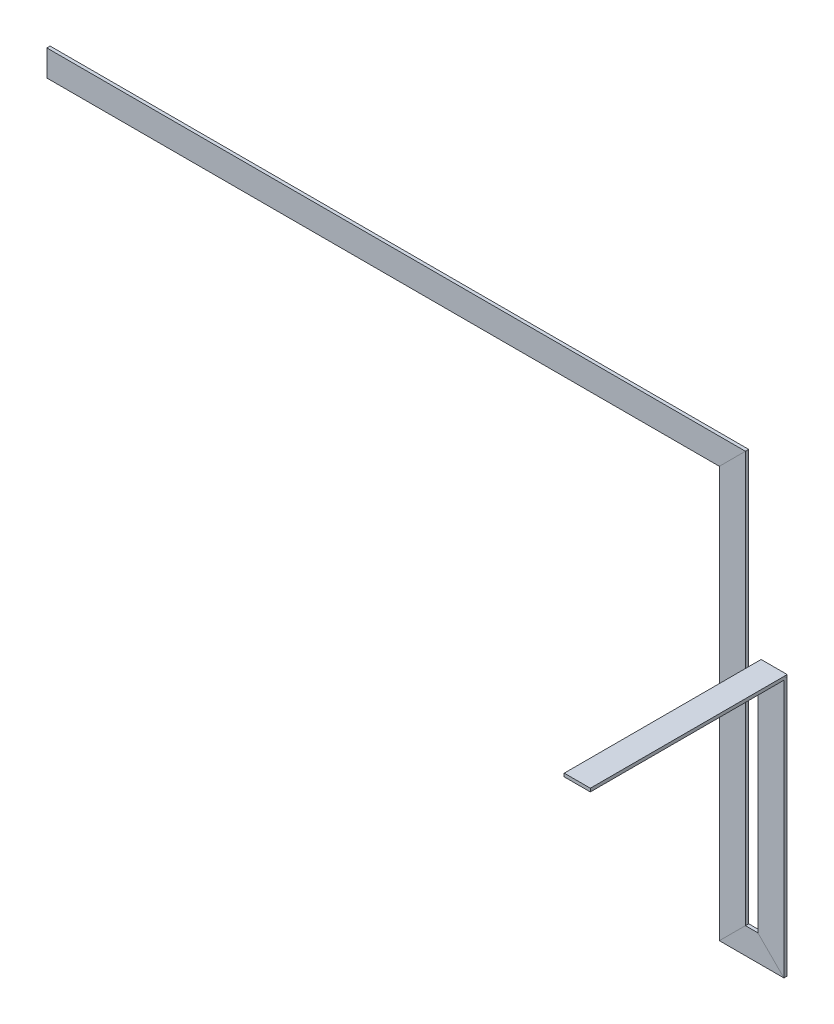
SolidWorks part; units mm, degrees
ref_plane "Alzado" through (0, 0, 0) normal (0, 0, 1) x (1, 0, 0)
ref_plane "Planta" through (0, 0, 0) normal (0, 1, 0) x (1, 0, 0)
ref_plane "Vista lateral" through (0, 0, 0) normal (1, 0, 0) x (0, 0, -1)
sketch3d "Croquis3D2"
  line L0 (62.2909, 217.5, 0) -> (62.2909, -251.2055, 0) construction
  line L1 (62.2909, -251.2055, 0) -> (-13.6009, -251.2055, 0) construction
  line L2 (-13.6009, -251.2055, 0) -> (-13.6009, 422.1421, 0) construction
  line L3 (-227.7091, 422.5, -94.9926) -> (-101.7371, 422.5, -94.9926) construction
  line L4 (-13.6009, 422.1421, 0) -> (-13.6009, 482.7109, 0) construction
  line L5 (-13.6009, 482.7109, 0) -> (-1290.2449, 482.7109, 0) construction
  line L6 (62.2909, 217.5, 0) -> (62.2909, 217.5, 73.9146)
  line L7 (62.2909, 217.5, 73.9146) -> (62.2909, -262.5, 73.9146)
  line L8 (62.2909, -262.5, 73.9146) -> (-12.7091, -262.5, 73.9146)
  line L9 (-12.7091, -262.5, 73.9146) -> (-12.7091, 537.5, 73.9146)
  line L10 (-12.7091, 537.5, 73.9146) -> (-1347.7009, 537.5, 73.9146)
  dimension "D1" = 800
  dimension "D2" = 75
  dimension "D3" = 480
  dimension "D4" = 1334.9917
sketch "Croquis3" plane through (0, 0, 0) normal (0, 0, 1) x (1, 0, 0)
  line L1 (36.8909, 220.675) -> (87.6909, 220.675)
  line L2 (36.8909, 220.675) -> (36.8909, 214.325)
  line L3 (36.8909, 214.325) -> (87.6909, 214.325)
  line L4 (87.6909, 220.675) -> (87.6909, 214.325)
  line L5 (36.8909, 220.675) -> (87.6909, 214.325) construction
  line L6 (36.8909, 214.325) -> (87.6909, 220.675) construction
  point P0 (62.2909, 217.5)
  dimension "D1" = 50.8
  dimension "D2" = 6.35
sweep "Barrer1" add profiles "Croquis3" path "Croquis3D2"
ref_plane "Plano1" through (62.2909, 0, 0) normal (1, 0, 0) x (0, 0, -1)
sketch "Croquis4" plane through (0, 0, 77.0896) normal (0, 0, 1) x (1, 0, 0)
  line L0 (36.8909, 220.675) -> (36.8909, 214.325)
  line L1 (36.8909, 214.325) -> (87.6909, 214.325)
  line L2 (87.6909, 214.325) -> (87.6909, 220.675)
  line L3 (87.6909, 220.675) -> (36.8909, 220.675)
extrude "Saliente-Extruir1" add sketch "Croquis4" along normal blind 377
sketch "Croquis5" plane through (0, 220.675, 0) normal (0, 1, 0) x (1, 0, 0)
  line L0 (36.8909, -77.0896) -> (36.8909, -70.7396) construction
  line L1 (36.8909, -70.7396) -> (87.6909, -70.7396)
  line L2 (87.6909, 0) -> (87.6909, -77.0896) construction
  line L3 (87.6909, -70.7396) -> (87.6909, 0)
  line L4 (87.6909, 0) -> (36.8909, 0)
  line L5 (36.8909, 0) -> (36.8909, -70.7396)
extrude "Cortar-Extruir1" cut sketch "Croquis5" against normal blind 8
